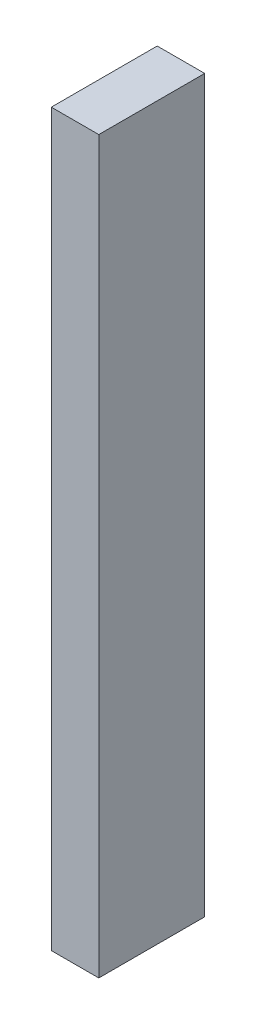
SolidWorks part; units mm, degrees
ref_plane "Front Plane" through (0, 0, 0) normal (0, 0, 1) x (1, 0, 0)
ref_plane "Top Plane" through (0, 0, 0) normal (0, 1, 0) x (1, 0, 0)
ref_plane "Right Plane" through (0, 0, 0) normal (1, 0, 0) x (0, 0, -1)
sketch "Sketch1" plane through (0, 0, 0) normal (0, 0, 1) x (1, 0, 0)
  line L1 (-6.5, 100) -> (6.5, 100)
  line L2 (-6.5, 100) -> (-6.5, -100)
  line L3 (-6.5, -100) -> (6.5, -100)
  line L4 (6.5, 100) -> (6.5, -100)
  line L5 (-6.5, 100) -> (6.5, -100) construction
  line L6 (-6.5, -100) -> (6.5, 100) construction
  point P0 (0, 0)
  dimension "D1" = 200
  dimension "D2" = 13
extrude "Boss-Extrude1" add sketch "Sketch1" along normal blind 29
